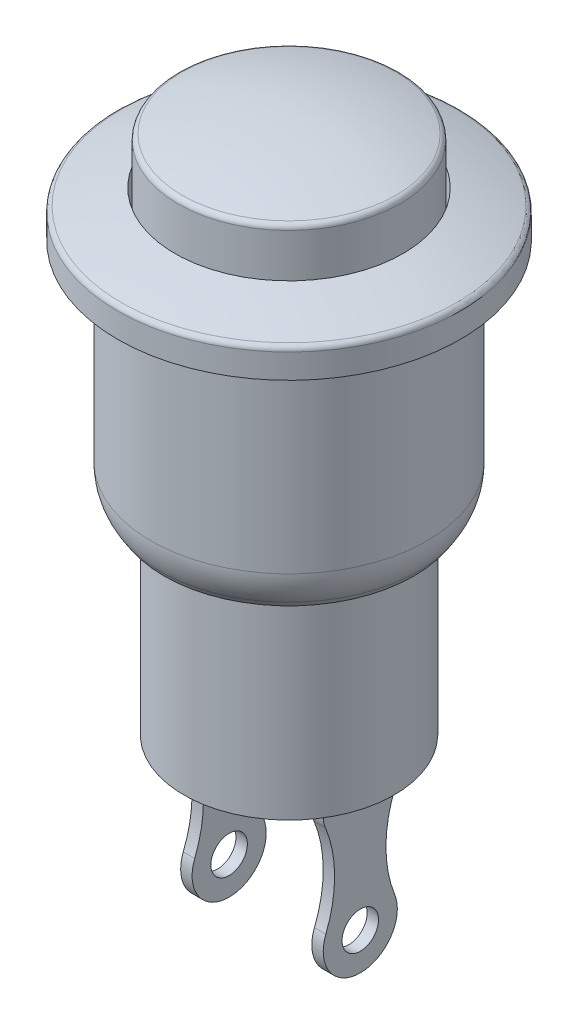
SolidWorks part; units mm, degrees
ref_plane "Plan de face" through (0, 0, 0) normal (0, 0, 1) x (1, 0, 0)
ref_plane "Plan de dessus" through (0, 0, 0) normal (0, 1, 0) x (1, 0, 0)
ref_plane "Plan de droite" through (0, 0, 0) normal (1, 0, 0) x (0, 0, -1)
sketch "Esquisse1" plane through (0, 0, 0) normal (0, 0, 1) x (1, 0, 0)
  line L0 (0, 0) -> (0, 22.281) construction
  line L1 (0, 0) -> (3.69, 0)
  line L2 (3.69, 0) -> (3.69, 7)
  line L3 (3.69, 7) -> (4.84, 7)
  line L4 (4.84, 7) -> (4.84, 15)
  line L5 (4.84, 15) -> (6.01, 15)
  line L6 (6.01, 15) -> (6.01, 16)
  line L7 (4, 16.6) -> (4, 15.0132)
  line L8 (4, 28.4891) -> (4, 11.2832) construction
  line L9 (4, 15.0132) -> (3.89, 15.0132)
  line L10 (3.89, 15.0132) -> (3.89, 18.2)
  line L11 (-3.8266, 18.8) -> (12.3412, 18.8) construction
  line L12 (0, 0) -> (0, -31.1321) construction
  line L13 (0, 18.8) -> (0, 0)
  arc A0 (4, 18.1647) -> (0, 18.8) centre (0, 5.8899) ccw
  arc A1 (6.01, 16) -> (4, 16.6) centre (0, -0.4667) ccw
  point P15 (4, 16.6)
  point P21 (0, 18.8)
  dimension "D1" = 7
  dimension "D2" = 7.38
  dimension "D3" = 9.68
  dimension "D4" = 8
  dimension "D5" = 18.2
  dimension "D6" = 12.02
  dimension "D7" = 1
  dimension "D8" = 4
  dimension "D9" = 18.8
  dimension "D10" = 7.78
  dimension "D11" = 16.6
  dimension "D12" = 15.0132
revolve "Révolution1" add sketch "Esquisse1" angle 360 about L0
fillet "Congé1" radius 0.2 1 edges at (0, 18.2, -3.89)
fillet "Congé2" radius 0.2 1 edges at (0, 16, -6.01)
chamfer "Chanfrein1" distance 0.7 angle 33 1 edges at (0, 7, -4.84)
fillet "Congé3" radius 2 1 edges at (0, 7.7, -4.84)
sketch "Esquisse2" plane through (0, 0, 0) normal (0, -1, 0) x (1, 0, 0)
  line L0 (0, 0) -> (0, 6.3616) construction
  line L1 (2.1, 1.3) -> (2.1, -1.3)
  line L2 (-2.5, 1.3) -> (-2.1, 1.3)
  line L3 (-2.5, 1.3) -> (-2.5, -1.3)
  line L4 (-2.5, -1.3) -> (-2.1, -1.3)
  line L5 (-2.1, 1.3) -> (-2.1, -1.3)
  line L6 (2.5, -1.3) -> (2.1, -1.3)
  line L7 (2.5, 1.3) -> (2.5, -1.3)
  line L8 (2.5, 1.3) -> (2.1, 1.3)
  dimension "D1" = 0.4
  dimension "D2" = 2.6
  dimension "D3" = 1.3
  dimension "D4" = 2.5
extrude "Boss.-Extru.1" add sketch "Esquisse2" along normal blind 6
sketch "Esquisse3" plane through (-2.5, 0, 0) normal (-1, 0, 0) x (0, 0, 1)
  line L0 (-4.1925, -0.8) -> (5.2253, -0.8) construction
  line L1 (-3.69, 0) -> (3.69, 0) construction
  line L2 (-3.2571, -4) -> (5.3895, -4) construction
  line L3 (-1.3, -6) -> (-1.3, 0) construction
  line L4 (1.3, -6) -> (1.3, 0) construction
  line L5 (1.3, -6) -> (-1.3, -6) construction
  line L6 (0, 0) -> (0, -6.5355) construction
  line L7 (1.3, 0) -> (-1.3, 0) construction
  line L8 (-0.9, -1.0754) -> (-0.9, -4.4649) construction
  line L9 (-1.3, -0.8) -> (-4.1925, -0.8)
  line L10 (-4.1925, -0.8) -> (-4.1925, -7.4756)
  line L11 (-4.1925, -7.4756) -> (5.5728, -7.5751)
  line L12 (5.5728, -7.5751) -> (5.2253, -0.8)
  line L13 (5.2253, -0.8) -> (1.3, -0.8)
  arc A0 (-1.2076, -4.2185) -> (1.2076, -4.2185) centre (0, -4.7) ccw
  arc A1 (-1.2076, -4.2185) -> (-1.3, -0.8) centre (-5.2253, -2.6167) ccw
  arc A2 (1.2076, -4.2185) -> (1.3, -0.8) centre (5.2253, -2.6167) cw
  circle A3 centre (0, -4.7) radius 0.64
  point P5 (-4.3046, -0.8)
  point P14 (-1.3, -0.8)
  point P32 (5.3895, -4)
  point P35 (5.1329, -0.8)
  dimension "D3" = 1.28
  dimension "D1" = 0.8
  dimension "D2" = 4
  dimension ".9" = 0.9
  dimension "D4" = 6.5253
  dimension "D5" = 6.8728
  dimension "D6" = 2.8925
  dimension "D7" = 7.4756
  dimension "D8" = 7.5751
extrude "Enlèv. mat.-Extru.1" cut sketch "Esquisse3" against normal blind 6
fillet "Congé4" radius 1 4 edges at (2.3, -0.8, 1.3) (-2.3, -0.8, 1.3) (2.3, -0.8, -1.3) (-2.3, -0.8, -1.3)
